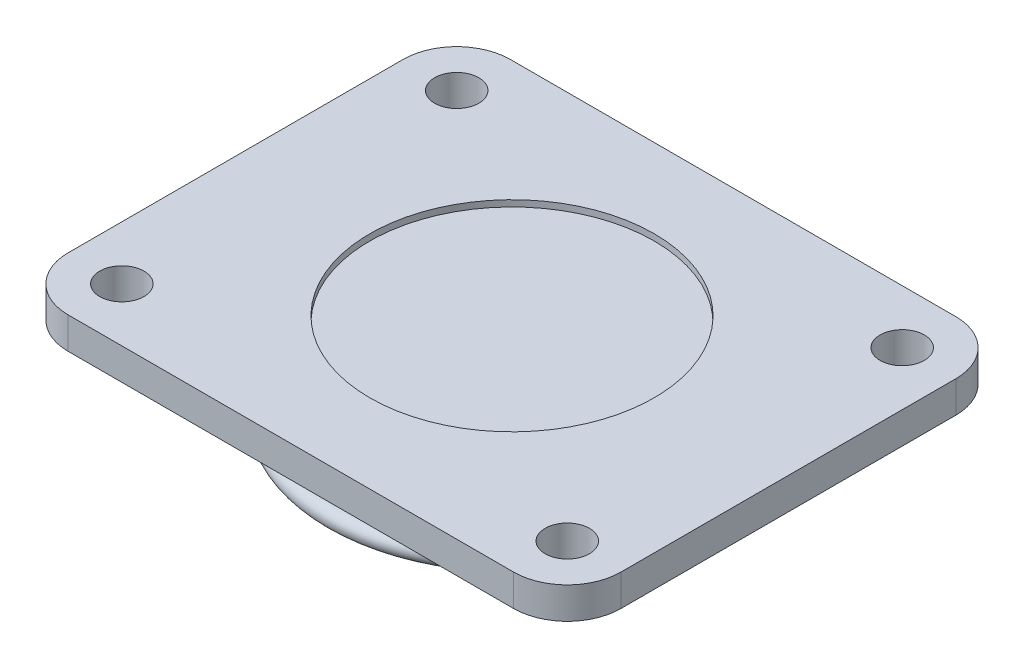
SolidWorks part; units mm, degrees
material "AISI 316 Stainless Steel Sheet (SS)"
ref_plane "Front Plane" through (0, 0, 0) normal (0, 0, 1) x (1, 0, 0)
ref_plane "Top Plane" through (0, 0, 0) normal (0, 1, 0) x (1, 0, 0)
ref_plane "Right Plane" through (0, 0, 0) normal (1, 0, 0) x (0, 0, -1)
sketch "Sketch1" plane through (0, 0, 0) normal (0, 1, 0) x (1, 0, 0)
  line L1 (-70.5, -70) -> (70.5, -70)
  line L2 (-87.5, -53) -> (-87.5, 53)
  line L3 (-70.5, 70) -> (70.5, 70)
  line L4 (87.5, -53) -> (87.5, 53)
  line L5 (-87.5, -70) -> (87.5, 70) construction
  line L6 (-87.5, 70) -> (87.5, -70) construction
  arc A0 (70.5, 70) -> (87.5, 53) centre (70.5, 53) cw
  arc A1 (70.5, -70) -> (87.5, -53) centre (70.5, -53) ccw
  arc A2 (-70.5, -70) -> (-87.5, -53) centre (-70.5, -53) cw
  arc A3 (-87.5, 53) -> (-70.5, 70) centre (-70.5, 53) cw
  circle A4 centre (-70.5, 53) radius 7
  circle A5 centre (-70.5, -53) radius 7
  circle A6 centre (70.5, -53) radius 7
  circle A7 centre (70.5, 53) radius 7
  point P0 (0, 0)
  dimension "D3" = 17
  dimension "D4" = 14
  dimension "D1" = 175
  dimension "D2" = 140
extrude "Boss-Extrude1" add sketch "Sketch1" along normal blind 10
sketch "Sketch2" plane through (0, 0, 0) normal (0, -1, 0) x (1, 0, 0)
  circle A0 centre (0, 0) radius 56
  dimension "D1" = 112
extrude "Boss-Extrude2" add sketch "Sketch2" along normal blind 20
sketch "Sketch3" plane through (0, 0, 0) normal (1, 0, 0) x (0, 0, -1)
  line L0 (-56, 0) -> (-56, -20) construction
  line L1 (-56, -20) -> (56, -20) construction
  line L2 (0, 0) -> (0, -20) construction
  circle A0 centre (-56, -17) radius 3
  dimension "D1" = 6
revolve "Revolve1" add sketch "Sketch3" angle 360 about L2
sketch "Sketch4" plane through (0, -20, 0) normal (0, -1, 0) x (1, 0, 0)
  circle A0 centre (0, 0) radius 7.5
  dimension "D1" = 15
extrude "Boss-Extrude3" add sketch "Sketch4" along normal blind 25
cosmetic thread "Cosmetic Thread1" parameters "D2"=0.911
chamfer "Chamfer1" distance 1 angle 45 1 edges at (0, -45, -7.5)
sketch "Sketch5" plane through (0, 10, 0) normal (0, 1, 0) x (1, 0, 0)
  circle A0 centre (0, 0) radius 45
  dimension "D1" = 90
extrude "Cut-Extrude1" cut sketch "Sketch5" against normal blind 2
scale "Scale1" scale about centroid uniform scaling yes scale factor 0.18
scale "Scale2" scale about centroid uniform scaling yes scale factor 1.04
